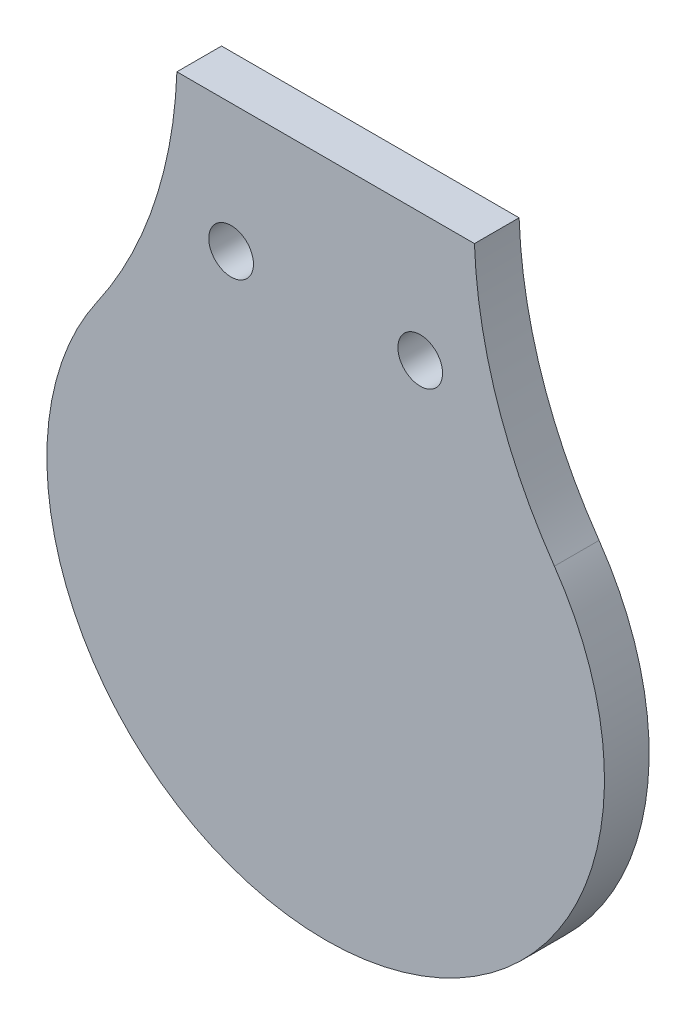
SolidWorks part; units mm, degrees
ref_plane "Front Plane" through (0, 0, 0) normal (0, 0, 1) x (1, 0, 0)
ref_plane "Top Plane" through (0, 0, 0) normal (0, 1, 0) x (1, 0, 0)
ref_plane "Right Plane" through (0, 0, 0) normal (1, 0, 0) x (0, 0, -1)
sketch "Sketch1" plane through (0, 0, 0) normal (0, 0, 1) x (1, 0, 0)
  line L0 (-16.9235, -361.9327) -> (16.9235, -361.9327)
  arc A0 (-26.0165, -389.1645) -> (26.0165, -389.1645) centre (0, -407.2996) ccw
  arc A3 (16.9235, -361.9327) -> (26.0165, -389.1645) centre (67.691, -360.115) ccw
  arc A4 (-26.0165, -389.1645) -> (-16.9235, -361.9327) centre (-67.691, -360.115) ccw
  circle A5 centre (-10.7564, -376.5256) radius 2.54
  circle A6 centre (10.7564, -376.5256) radius 2.54
extrude "Boss-Extrude1" add sketch "Sketch1" along normal blind 5.08
